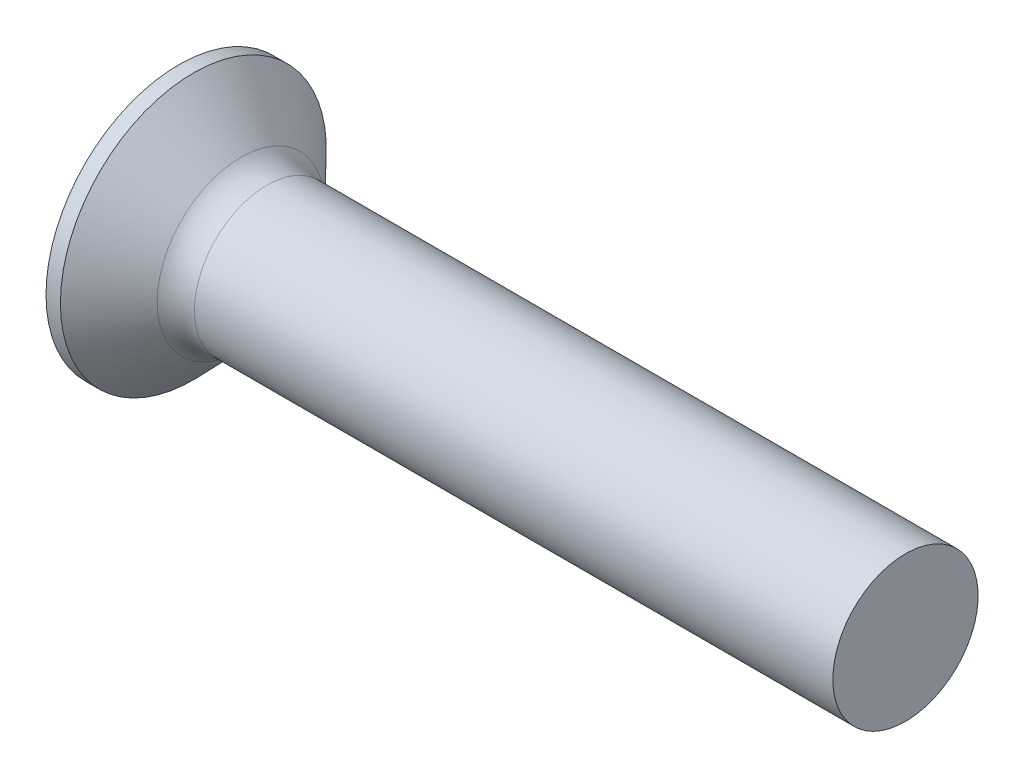
SolidWorks part; units mm, degrees
revolve "Base-Revolve" add sketch "BodySke"
sketch "BodySke" plane through (0, 0, 0) normal (0, 0, 1) x (1, 0, 0)
  line L0 (0, 0) -> (0, 9.15)
  line L1 (0, 9.15) -> (0.9924, 9.15)
  line L2 (5, 5) -> (50, 5)
  line L3 (50, 5) -> (50, 0)
  line L4 (50, 0) -> (0, 0)
  line L5 (-6.35, 0) -> (82.55, 0) construction
  line L6 (5, -5) -> (50, -5) construction
  line L7 (0.9924, -9.15) -> (5, -5) construction
  line L8 (0.9924, 9.15) -> (5, 5)
  line L9 (0, -9.15) -> (0.9924, -9.15) construction
  line L10 (6.5, 6.5875) -> (6.5, -2.9375) construction
  line L11 (0, 6.35) -> (0, -3.175) construction
cosmetic thread "ThreadCosmetic" [suppressed]
fillet "Fillet1" radius 2.5 1 edges at (5, 0, 5)
ref_plane "Plane1" through (0, 0, 0) normal (0, 0, 1) x (1, 0, 0)
ref_plane "Plane2" through (0, 0, 0) normal (0, 1, 0) x (1, 0, 0)
ref_plane "Plane3" through (0, 0, 0) normal (1, 0, 0) x (0, 0, -1)
sketch "Sketch3" plane through (0, 0, 0) normal (-1, 0, 0) x (0, 0, 1)
  line L0 (-1.08, 4.9) -> (1.08, 4.9)
  line L1 (1.08, 4.9) -> (1.08, -4.9)
  line L2 (1.08, -4.9) -> (-1.08, -4.9)
  line L3 (-1.08, -4.9) -> (-1.08, 4.9)
  dimension "D1" = 2.45
  dimension "D2" = 0.515
ref_plane "Plane4" through (5.64, 0, 0) normal (-1, 0, 0) x (0, 0, 1)
sketch "Sketch4" plane through (5.64, 0, 0) normal (-1, 0, 0) x (0, 0, 1)
  line L0 (-1.08, 2.088) -> (1.08, 2.088)
  line L3 (1.08, 2.088) -> (1.08, -2.088)
  line L4 (1.08, -2.088) -> (-1.08, -2.088)
  line L5 (-1.08, -2.088) -> (-1.08, 2.088)
  dimension "D2" = 1.8587
  dimension "D1" = 1.03
  dimension "D4" = 0.9293
  dimension "D3" = 0.515
loft "Recess" cut profiles "Sketch3", "Sketch4"
pattern_circular "RecPat" count 2 every 90 about axis through (0, 0, 0) along (1, 0, 0) of "Recess"
sketch "RecCorSke" plane through (0, 0, 0) normal (0, 0, 1) x (1, 0, 0)
  line L0 (-3.175, 0) -> (15.875, 0) construction
  line L2 (0, 0) -> (0, 2.3249)
  line L3 (0, 2.3249) -> (5.64, 1.9305)
  line L4 (5.64, 1.9305) -> (6.2673, 0)
  line L5 (6.2673, 0) -> (0, 0)
  dimension "Depth" = 3.05
  dimension "Draft_angle" = 4
  dimension "Bottom_angle" = 18
revolve "RecessCore" cut sketch "RecCorSke" angle 360 about L0
sketch "ThdSchSke" plane through (0, 0, 0) normal (0, 0, 1) x (1, 0, 0)
  line L0 (6.5, -3.9624) -> (5.7735, -5)
  line L1 (6.5, -3.9624) -> (7.2265, -5)
  line L2 (7.2265, -5) -> (7.2265, -6.25)
  line L3 (-3.175, 0) -> (5.1513, 0) construction
  line L5 (7.2265, -6.25) -> (5.7735, -6.25)
  line L6 (5.7735, -6.25) -> (5.7735, -5)
  line L7 (0, 9.15) -> (0, -9.15) construction
  dimension "Thread_minor" = 4.11
  dimension "Diameter" = 5
  dimension "Start" = 3.5
revolve "ThreadSchematic" [suppressed] cut sketch "ThdSchSke" angle 360 about L3
pattern_linear "ThdSchPat" [suppressed]
equation "\"D1@Sketch3\" = \"Cross_dia@Sketch3\" / 2"
equation "\"D2@Sketch3\" = \"Cross_width@Sketch3\" / 2"
equation "\"Depth@RecCorSke\" = \"Cross_depth@Plane4\""
equation "\"D1@Sketch4\" = \"Cross_width@Sketch3\""
equation "\"D2@Sketch4\" = \"Cross_dia@Sketch3\" - 2.0 * \"Cross_depth@Plane4\" * tan(26.5  * 0.017453292)"
equation "\"D3@Sketch4\" = \"D1@Sketch4\" / 2"
equation "\"D4@Sketch4\" = \"D2@Sketch4\" / 2"
equation "\"Thread_length@ThreadCosmetic\" = ((sgn( (\"Length@BodySke\" - \"Advance@BodySke\" * 1.0 - \"Head_ht@BodySke\" ) - \"Thread_nom@BodySke\" )-1)*( (\"Length@BodySke\" - \"Advance@BodySke\" * 1.0 - \"Head_ht@BodySke\" ) - \"Thread_nom@BodySke\" ))/-2+ \"Thread_nom@BodySke\""
equation "\"Thread_minor@ThdSchSke\" = \"Thread_minor@ThreadCosmetic\""
equation "\"Diameter@ThdSchSke\" = \"Diameter@BodySke\""
equation "\"Overcut@ThdSchSke\" = \"Diameter@BodySke\" * 1.25"
equation "\"Start@ThdSchSke\" = 0.000001 + \"Length@BodySke\" - \"Thread_length@ThreadCosmetic\"  '---Countersunk---"
equation "\"Num_threads@ThdSchPat\" = int( \"Thread_length@ThreadCosmetic\" / \"Advance@BodySke\" + 0.999 )  + 1"
equation "\"Advance@ThdSchPat\" = \"Thread_length@ThreadCosmetic\" /  (\"Num_threads@ThdSchPat\" - 1) 'relax it"
